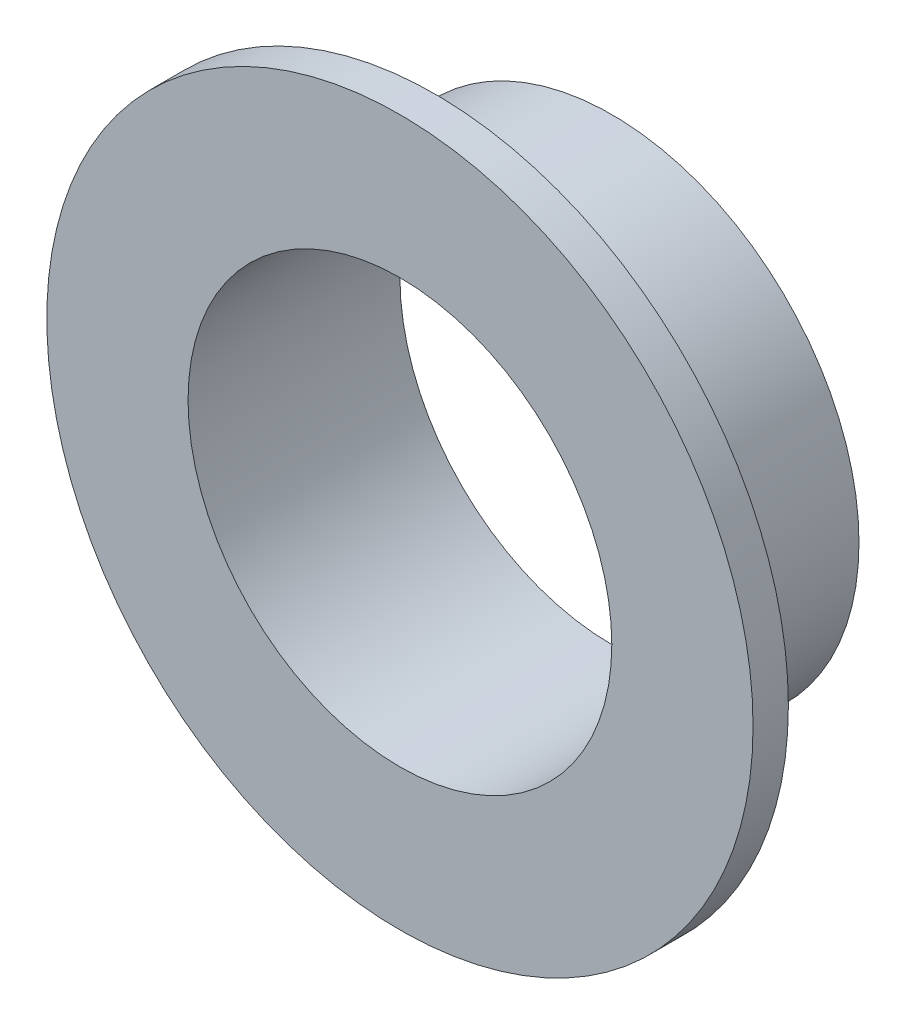
SolidWorks part; units mm, degrees
ref_plane "Front Plane" through (0, 0, 0) normal (0, 0, 1) x (1, 0, 0)
ref_plane "Top Plane" through (0, 0, 0) normal (0, 1, 0) x (1, 0, 0)
ref_plane "Right Plane" through (0, 0, 0) normal (1, 0, 0) x (0, 0, -1)
sketch "Sketch1" plane through (0, 0, 0) normal (0, 0, 1) x (1, 0, 0)
  circle A0 centre (0, 0) radius 6
  circle A1 centre (0, 0) radius 7
  dimension "D1" = 12
  dimension "D2" = 14
extrude "Boss-Extrude1" add sketch "Sketch1" along normal blind 5
sketch "Sketch3" plane through (0, 0, 5) normal (0, 0, 1) x (1, 0, 0)
  circle A0 centre (0, 0) radius 6
  circle A1 centre (0, 0) radius 10
  dimension "D1" = 20
extrude "Boss-Extrude2" add sketch "Sketch3" along normal blind 1
